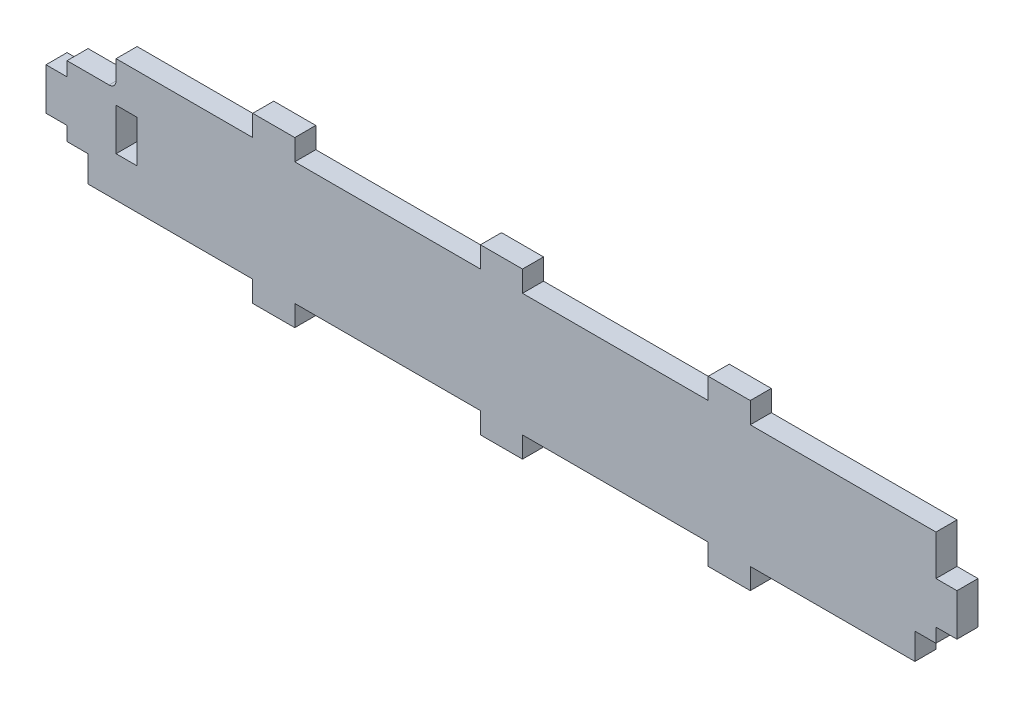
SolidWorks part; units mm, degrees
ref_plane "Front Plane" through (0, 0, 0) normal (0, 0, 1) x (1, 0, 0)
ref_plane "Top Plane" through (0, 0, 0) normal (0, 1, 0) x (1, 0, 0)
ref_plane "Right Plane" through (0, 0, 0) normal (1, 0, 0) x (0, 0, -1)
sketch "Sketch2" plane through (0, 0, 0) normal (0, 1, 0) x (1, 0, 0)
  line L0 (0, 0) -> (0, 6) construction
  dimension "D1" = 6
sketch "Sketch1" plane through (0, 0, 0) normal (0, 0, 1) x (1, 0, 0)
  line L1 (-130, -23.5) -> (130, -23.5)
  line L2 (-130, -23.5) -> (-130, 23.5)
  line L3 (-130, 23.5) -> (130, 23.5)
  line L4 (130, -23.5) -> (130, 23.5)
  line L5 (-130, -23.5) -> (130, 23.5) construction
  line L6 (-130, 23.5) -> (130, -23.5) construction
  point P0 (0, 0)
  dimension "D1" = 260
  dimension "D2" = 47
extrude "Boss-Extrude1" add sketch "Sketch1" against normal up to vertex (6 mm away) contours L2 L3 L4 L1 up to point (0, 0, -6)
sketch "Sketch3" plane through (0, 0, 0) normal (0, 0, 1) x (1, 0, 0)
  line L0 (-130, -23.5) -> (130, -23.5) construction
  line L1 (-130, 23.5) -> (-124, 23.5)
  line L2 (-130, 23.5) -> (-130, -23.5)
  line L3 (-130, -23.5) -> (-124, -23.5)
  line L4 (-124, 23.5) -> (-124, -23.5)
  line L5 (-110, 23.5) -> (-110, -23.5) construction
  line L6 (130, 23.5) -> (124, 23.5)
  line L7 (130, 23.5) -> (130, -23.5)
  line L8 (130, -23.5) -> (124, -23.5)
  line L9 (124, 23.5) -> (124, -23.5)
  line L10 (-124, 10) -> (124, 10) construction
  line L11 (-124, 10) -> (-124, -10) construction
  line L12 (-124, -10) -> (124, -10) construction
  line L13 (124, 10) -> (124, -10) construction
  line L14 (0, -10) -> (0, 10) construction
  line L15 (-130, 23.5) -> (130, 23.5) construction
  line L16 (-110, 23.5) -> (-104, 23.5) construction
  line L17 (-104, 23.5) -> (-104, -23.5) construction
  line L18 (-104, -23.5) -> (-110, -23.5) construction
  line L19 (-124, 0) -> (-130, 0) construction
  line L20 (-124, 6) -> (-130, 6)
  line L21 (-124, 6) -> (-124, -6)
  line L22 (-124, -6) -> (-130, -6)
  line L23 (-130, 6) -> (-130, -6)
  line L24 (-118, -10) -> (-118, -17.5)
  line L25 (-118, -17.5) -> (-124, -17.5)
  line L26 (-118, -17.5) -> (-118, -23.5)
  line L27 (-110, 23.5) -> (-110, 17.5) construction
  line L28 (-110, 17.5) -> (-124, 17.5) construction
  line L29 (-118, -17.5) -> (-110, -17.5) construction
  line L33 (-118, -10) -> (-124, -10)
  line M26 (-130, -23.5) -> (130, -23.5)
  line M28 (130, 23.5) -> (-130, 23.5)
  line M29 (-130, 23.5) -> (-130, -23.5)
  dimension "D1" = 6
  dimension "D2" = 20
  dimension "D3" = 14
  dimension "D4" = 12
  dimension "D5" = 6
  dimension "D6" = 7.5
  dimension "D7" = 8
extrude "Cut-Extrude1" cut sketch "Sketch3" against normal through all contours L20 L4 M28 M29 | L4 L22 M29 M26 | L24 L33 L4 L25
mirror "Mirror1" about plane through (0, 0, 0) normal (1, 0, 0) of "Cut-Extrude1"
sketch "Sketch4" plane through (0, 0, 0) normal (0, 0, 1) x (1, 0, 0)
  line L0 (-130, -23.5) -> (130, -23.5) construction
  line L1 (-6, -17.5) -> (6, -17.5) construction
  line L2 (-6, -17.5) -> (-6, -23.5) construction
  line L3 (-6, -23.5) -> (6, -23.5) construction
  line L4 (6, -17.5) -> (6, -23.5) construction
  line L5 (-124, -17.5) -> (-71, -17.5) construction
  line L6 (59, -17.5) -> (71, -17.5) construction
  line L7 (59, -17.5) -> (59, -23.5) construction
  line L8 (59, -23.5) -> (71, -23.5) construction
  line L9 (71, -17.5) -> (71, -23.5) construction
  line L10 (-59, -17.5) -> (-71, -17.5) construction
  line L11 (-59, -17.5) -> (-59, -23.5) construction
  line L12 (-59, -23.5) -> (-71, -23.5) construction
  line L13 (-71, -17.5) -> (-71, -23.5) construction
  line L14 (-59, -17.5) -> (-6, -17.5) construction
  line L15 (59, -17.5) -> (6, -17.5) construction
  line L16 (71, -17.5) -> (124, -17.5) construction
  line L19 (-124, -17.5) -> (-71, -17.5)
  line L20 (-124, -17.5) -> (-124, -23.5)
  line L21 (-124, -23.5) -> (-71, -23.5)
  line L22 (-71, -17.5) -> (-71, -23.5)
  line L23 (-59, -23.5) -> (-6, -23.5)
  line L24 (-59, -23.5) -> (-59, -17.5)
  line L25 (-59, -17.5) -> (-6, -17.5)
  line L26 (-6, -23.5) -> (-6, -17.5)
  line L27 (6, -17.5) -> (59, -17.5)
  line L28 (6, -17.5) -> (6, -23.5)
  line L29 (6, -23.5) -> (59, -23.5)
  line L30 (59, -17.5) -> (59, -23.5)
  line L31 (71, -23.5) -> (124, -23.5)
  line L32 (71, -23.5) -> (71, -17.5)
  line L33 (71, -17.5) -> (124, -17.5)
  line L34 (124, -23.5) -> (124, -17.5)
  line M36 (-118, -17.5) -> (-124, -17.5)
  line M37 (-124, -17.5) -> (-124, -23.5)
  line M38 (-124, -23.5) -> (124, -23.5)
  line M39 (124, -23.5) -> (124, -17.5)
  line M40 (124, -17.5) -> (118, -17.5)
  dimension "D1" = 12
extrude "Cut-Extrude2" cut sketch "Sketch4" against normal through all contours L22 L19 M36 M37 M38 | L26 L25 L24 M38 | L30 L27 L28 M38 | L33 L32 M38 M39 M40
mirror "Mirror2" about plane through (0, 0, 0) normal (0, 1, 0) of "Cut-Extrude2"
sketch "Sketch5" plane through (0, 0, 0) normal (0, 0, 1) x (1, 0, 0)
  line L0 (-110, 23.5) -> (-110, -23.5) construction
  line L1 (-110, 17.5) -> (-124, 17.5)
  line L2 (-110, 17.5) -> (-110, 10)
  line L3 (-110, 10) -> (-124, 10)
  line L4 (-124, 17.5) -> (-124, 10)
  line L5 (-110, 6) -> (-104, 6)
  line L6 (-110, 6) -> (-110, -6)
  line L7 (-110, -6) -> (-104, -6)
  line L8 (-104, 6) -> (-104, -6)
  line L9 (-104, 23.5) -> (-104, -23.5) construction
  line L10 (-124, 6) -> (-130, 6) construction
  line L11 (-124, -6) -> (-130, -6) construction
extrude "Cut-Extrude3" cut sketch "Sketch5" against normal through all
fillet "Fillet1" radius 2 1 edges at (-110, 10, -3)
equation "\"t_wood\"= 6' Thickness of the wood"
equation "\"t_glass\"= 2.5'Thickness of glass panels"
equation "\"w_glass\"= 248"
equation "\"h_glass\"= 167"
equation "\"h_food_internal\" = 60"
equation "\"entry_height\"= 20"
equation "\"entry diameter\"= 8"
equation "\"glass_bottom_overlap\"= 8"
equation "\"default_finger_size\"= 12"
equation "\"brood_depth\"= 42"
equation "\"outer_box_depth\" = \"brood_depth\" + ( 2 * \"t_glass\" ) + ( 2 * \"t_wood\" )"
equation "\"outer_box_width\"= \"w_glass\" + ( 2 * \"t_wood\" )"
equation "\"food_top_clearance\"= 10"
equation "\"outer_box_height\"= \"t_wood\" + \"h_glass\" + \"t_wood\" + \"h_food_internal\" + \"food_top_clearance\" + \"t_wood\""
equation "\"food_internal_depth\"= \"brood_depth\" + \"t_glass\" + \"t_glass\" - \"t_wood\" - \"t_wood\""
equation "\"food_channel_clearance_width\"= 14"
equation "\"bar_top_play\"= 4.5"
equation "\"bar_entry_angle\"= 10"
equation "\"bar_width\"= 20"
equation "\"entry_disk_play\"= 0.3"
equation "\"D1@Sketch2\"=\"t_wood\""
equation "\"D1@Sketch1\"=\"outer_box_width\""
equation "\"D2@Sketch1\"=\"brood_depth\"+\"t_glass\"+\"t_glass\""
equation "\"D1@Sketch3\"=\"t_wood\""
equation "\"D2@Sketch3\"=\"bar_width\""
equation "\"D3@Sketch3\"=\"food_channel_clearance_width\""
equation "\"D4@Sketch3\"=\"default_finger_size\""
equation "\"D5@Sketch3\"=\"t_wood\""
equation "\"D1@Sketch4\"=\"default_finger_size\""
